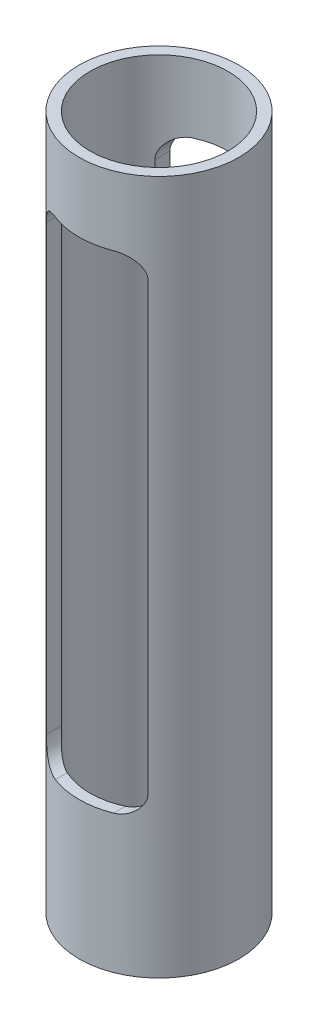
SolidWorks part; units mm, degrees
material "Aluminum Bronze"
ref_plane "Front Plane" through (0, 0, 0) normal (0, 0, 1) x (1, 0, 0)
ref_plane "Top Plane" through (0, 0, 0) normal (0, 1, 0) x (1, 0, 0)
ref_plane "Right Plane" through (0, 0, 0) normal (1, 0, 0) x (0, 0, -1)
sketch "Sketch1" plane through (0, 0, 0) normal (0, 1, 0) x (1, 0, 0)
  circle A0 centre (0, 0) radius 9.5
  circle A1 centre (0, 0) radius 11
extrude "Boss-Extrude1" add sketch "Sketch1" along normal blind 95.5
sketch "Sketch2" plane through (0, 0, 0) normal (0, 0, 1) x (1, 0, 0)
  line L0 (0, 86) -> (0, 95.5)
  line L1 (-4, 86) -> (4, 86)
  line L2 (-7, 83) -> (-7, 22)
  line L3 (-4, 19) -> (4, 19)
  line L4 (7, 83) -> (7, 22)
  line L5 (9.5, 95.5) -> (-9.5, 95.5) construction
  line L6 (11, 95.5) -> (-11, 95.5) construction
  line L7 (-11, 0) -> (11, 0) construction
  arc A0 (4, 19) -> (7, 22) centre (4, 22) ccw
  arc A1 (-4, 19) -> (-7, 22) centre (-4, 22) cw
  arc A2 (7, 83) -> (4, 86) centre (4, 83) ccw
  arc A3 (-7, 83) -> (-4, 86) centre (-4, 83) cw
  point P14 (7, 19)
  point P17 (-7, 19)
  point P22 (-7, 86)
  dimension "D4" = 3
  dimension "D1" = 19
  dimension "D2" = 67
  dimension "D3" = 14
extrude "Cut-Extrude1" cut sketch "Sketch2" against normal through all both and the other way through all contours A3 L2 A1 L3 A0 L4 A2 L1
